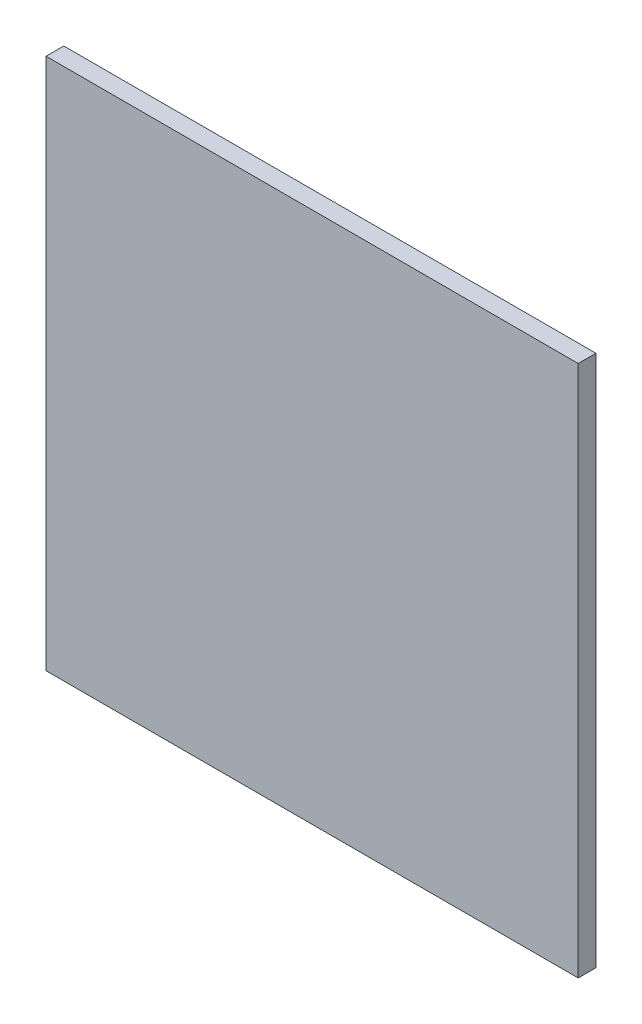
SolidWorks part; units mm, degrees
ref_plane "Front Plane" through (0, 0, 0) normal (0, 0, 1) x (1, 0, 0)
ref_plane "Top Plane" through (0, 0, 0) normal (0, 1, 0) x (1, 0, 0)
ref_plane "Right Plane" through (0, 0, 0) normal (1, 0, 0) x (0, 0, -1)
sketch "Sketch1" plane through (0, 0, 0) normal (0, 0, 1) x (1, 0, 0)
  line L1 (0, 0) -> (762, 0)
  line L2 (0, 0) -> (0, 762)
  line L3 (0, 762) -> (762, 762)
  line L4 (762, 0) -> (762, 762)
  dimension "D1" = 762
  dimension "D2" = 762
extrude "Boss-Extrude1" add sketch "Sketch1" along normal blind 25.4
